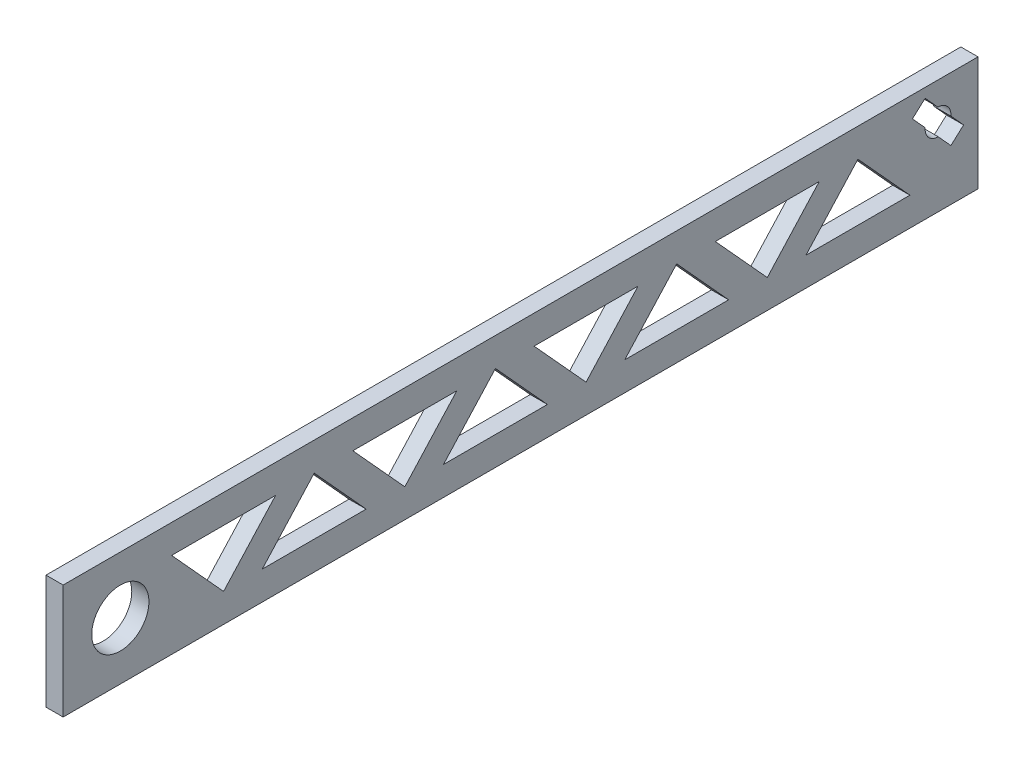
SolidWorks part; units mm, degrees
ref_plane "Front Plane" through (0, 0, 0) normal (0, 0, 1) x (1, 0, 0)
ref_plane "Top Plane" through (0, 0, 0) normal (0, 1, 0) x (1, 0, 0)
ref_plane "Right Plane" through (0, 0, 0) normal (1, 0, 0) x (0, 0, -1)
sketch "Sketch1" plane through (0, 0, 0) normal (1, 0, 0) x (0, 0, -1)
  line L1 (-160, -20) -> (160, -20)
  line L2 (-160, -20) -> (-160, 20)
  line L3 (-160, 20) -> (160, 20)
  line L4 (160, -20) -> (160, 20)
  line L5 (-160, -20) -> (160, 20) construction
  line L6 (-160, 20) -> (160, -20) construction
  circle A0 centre (-140, 0) radius 10
  point P0 (0, 0)
  dimension "D3" = 20
  dimension "D1" = 40
  dimension "D2" = 320
  dimension "D4" = 20
  dimension "D5" = 300
extrude "Boss-Extrude1" add sketch "Sketch1" along normal blind 6
sketch "Sketch2" plane through (0, 0, 0) normal (-1, 0, 0) x (0, 0, 1)
  line L0 (122.0617, 10) -> (103.8799, -10)
  line L1 (85.6981, 10) -> (103.8799, -10)
  line L2 (85.6981, 10) -> (122.0617, 10)
  line L3 (40.487, -20) -> (40.487, 5.1902) construction
  line L4 (-160, 20) -> (160, 20) construction
  line L5 (160, -20) -> (-160, -20) construction
  line L7 (20, -102.2679) -> (138.1818, 27.7321) construction
  line L8 (103.8799, -10) -> (103.8799, 10) construction
  line L9 (90.3653, -10) -> (54.0016, -10)
  line L10 (90.3653, -10) -> (72.1834, 10)
  line L11 (72.1834, 10) -> (72.1834, -10) construction
  line L12 (54.0016, -10) -> (72.1834, 10)
  line L13 (8.7906, 10) -> (8.7906, -10) construction
  line L14 (-22.9058, -10) -> (-22.9058, 10) construction
  line L15 (26.9724, -10) -> (8.7906, 10)
  line L16 (-9.3912, -10) -> (8.7906, 10)
  line L17 (-9.3912, -10) -> (26.9724, -10)
  line L18 (-4.724, 10) -> (-22.9058, -10)
  line L19 (-41.0876, 10) -> (-22.9058, -10)
  line L20 (-4.724, 10) -> (-41.0876, 10)
  line L21 (58.6688, 10) -> (40.487, -10)
  line L22 (22.3052, 10) -> (40.487, -10)
  line L23 (22.3052, 10) -> (58.6688, 10)
  line L24 (-54.6023, -20) -> (-54.6023, 7.4361) construction
  line L25 (20, -102.2679) -> (138.1818, 27.7321)
  line L26 (-131.5097, 10) -> (-149.6915, -10)
  line L27 (-131.5097, 10) -> (-149.6915, 10)
  line L28 (-99.8133, -10) -> (-136.1769, -10)
  line L29 (-136.1769, -10) -> (-117.9951, 10)
  line L30 (-99.8133, -10) -> (-117.9951, 10)
  line L31 (-104.4805, 10) -> (-86.2987, -10)
  line L32 (-104.4805, 10) -> (-68.1169, 10)
  line L33 (-68.1169, 10) -> (-86.2987, -10)
  line L34 (-36.4204, -10) -> (-72.7841, -10)
  line L35 (-72.7841, -10) -> (-54.6023, 10)
  line L36 (-36.4204, -10) -> (-54.6023, 10)
  line L37 (-149.6915, -10) -> (-149.6915, 10)
  dimension "D1" = 10
  dimension "D2" = 10
  dimension "D3" = 10
  dimension "D4" = 36.3636
  dimension "D5" = 68.0601
  dimension "D6" = 13.5146
  dimension "D7" = 13.5146
  dimension "D8" = 13.5146
extrude "Cut-Extrude2" cut sketch "Sketch2" against normal blind 10 contours L12 L9 L10 | L23 L22 L21 | L16 L17 L15 | L18 L20 L19 | L34 L36 L35 | L33 L32 L31 | L28 L30 L29 | L2 L0 L1
sketch "Sketch3" plane through (0, 0, 0) normal (-1, 0, 0) x (0, 0, 1)
  line L0 (-150.3536, -1.9515) -> (-137.2365, 12.4774) construction
  line L1 (-150.3536, -1.9515) -> (-137.2365, 12.4774) construction
  line L2 (-141.6761, 16.5134) -> (-154.7932, 2.0846) construction
  line L3 (-141.6761, 16.5134) -> (-154.7932, 2.0846) construction
  line L4 (-160, 20) -> (-132.0245, -5.4323) construction
  line L5 (-160, 20) -> (-132.0245, -5.4323) construction
  line L6 (-148.0303, 5.064) -> (-143.9942, 9.5037) construction
  line L7 (-148.0303, 5.064) -> (-143.9942, 9.5037) construction
  line L8 (-137.2365, 12.4774) -> (-141.6761, 16.5134) construction
  line L9 (-154.7932, 2.0846) -> (-150.3536, -1.9515) construction
  line L10 (-137.2365, 12.4774) -> (-141.6761, 16.5134) construction
  line L11 (-154.7932, 2.0846) -> (-150.3536, -1.9515) construction
  line L12 (-154.9614, 1.8996) -> (-150.5218, -2.1365)
  line L13 (-141.5027, 16.7042) -> (-137.0631, 12.6681)
  line L14 (-141.5027, 16.7042) -> (-145.9758, 11.7837)
  line L15 (-137.0631, 12.6681) -> (-141.5362, 7.7477)
  line L16 (-150.5218, -2.1365) -> (-150.365, -2.3415)
  line L17 (-146.0486, 2.784) -> (-150.5218, -2.1365)
  line L18 (-150.4883, 6.82) -> (-154.9614, 1.8996)
  arc A0 (-145.9758, 11.7837) -> (-150.4883, 6.82) centre (-146.0122, 7.2839) ccw
  arc A1 (-146.0486, 2.784) -> (-141.5362, 7.7477) centre (-146.0122, 7.2839) ccw
  dimension "D2" = 9
  dimension "D1" = 0.25
extrude "Cut-Extrude3" cut sketch "Sketch3" against normal through all contours L17 A1 L15 L13 L14 A0 L18 L12
equation "\"D7@Sketch2\"=\"D6@Sketch2\""
equation "\"D8@Sketch2\"=\"D6@Sketch2\""
